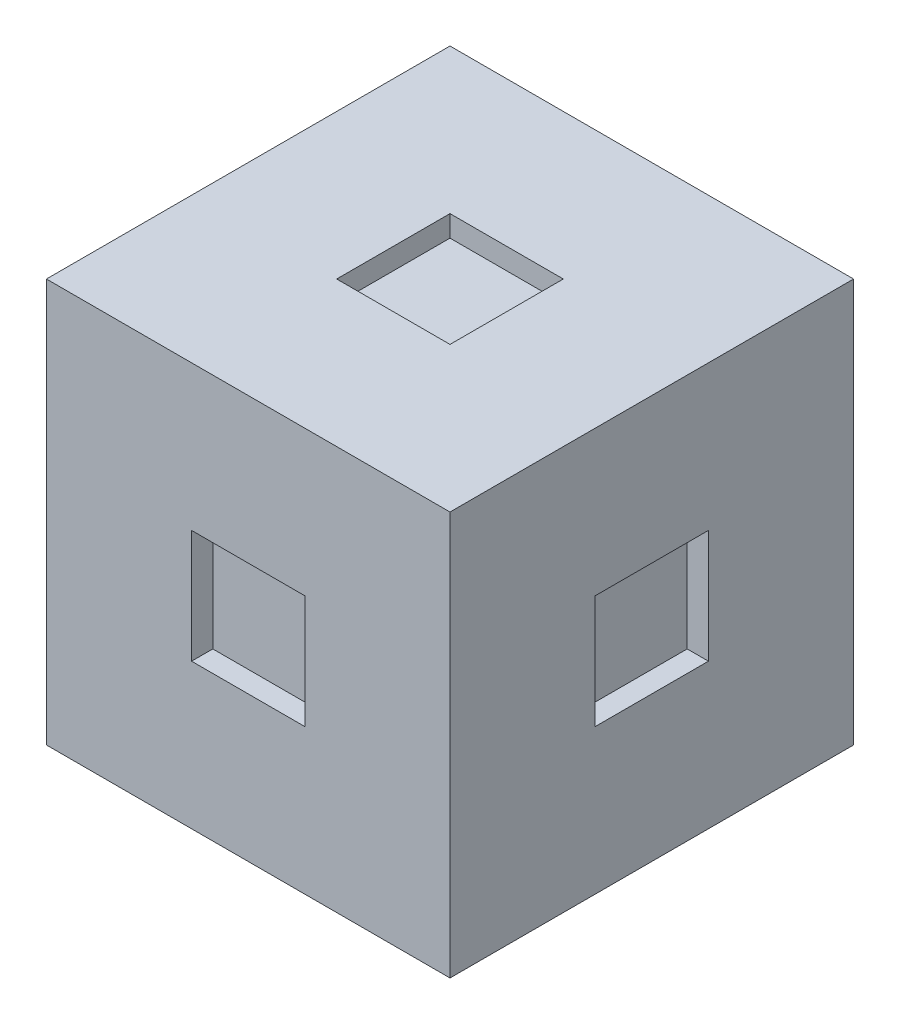
SolidWorks part; units mm, degrees
ref_plane "前视基准面" through (0, 0, 0) normal (0, 0, 1) x (1, 0, 0)
ref_plane "上视基准面" through (0, 0, 0) normal (0, 1, 0) x (1, 0, 0)
ref_plane "右视基准面" through (0, 0, 0) normal (1, 0, 0) x (0, 0, -1)
sketch "草图1" plane through (0, 0, 0) normal (0, 1, 0) x (1, 0, 0)
  line L1 (-28.5, 28.5) -> (28.5, 28.5)
  line L2 (-28.5, 28.5) -> (-28.5, -28.5)
  line L3 (-28.5, -28.5) -> (28.5, -28.5)
  line L4 (28.5, 28.5) -> (28.5, -28.5)
  line L5 (-28.5, 28.5) -> (28.5, -28.5) construction
  line L6 (-28.5, -28.5) -> (28.5, 28.5) construction
  point P0 (0, 0)
  dimension "D1" = 57
  dimension "D2" = 57
extrude "凸台-拉伸1" add sketch "草图1" along normal blind 57
sketch "草图2" plane through (0, 0, 28.5) normal (0, 0, 1) x (1, 0, 0)
  line L0 (-28.5, 57) -> (28.5, 0) construction
  line L1 (28.5, 57) -> (-28.5, 0) construction
  line L3 (-8, 36.5) -> (8, 36.5)
  line L4 (-8, 36.5) -> (-8, 20.5)
  line L5 (-8, 20.5) -> (8, 20.5)
  line L6 (8, 36.5) -> (8, 20.5)
  line L7 (-8, 36.5) -> (8, 20.5) construction
  line L8 (-8, 20.5) -> (8, 36.5) construction
  point P8 (0, 28.5)
  dimension "D1" = 16
extrude "切除-拉伸1" cut sketch "草图2" against normal blind 3
sketch "草图3" plane through (28.5, 0, 0) normal (1, 0, 0) x (0, 0, -1)
  line L0 (-28.5, 57) -> (28.5, 0) construction
  line L1 (28.5, 57) -> (-28.5, 0) construction
  line L3 (-8, 36.5) -> (8, 36.5)
  line L4 (-8, 36.5) -> (-8, 20.5)
  line L5 (-8, 20.5) -> (8, 20.5)
  line L6 (8, 36.5) -> (8, 20.5)
  line L7 (-8, 36.5) -> (8, 20.5) construction
  line L8 (-8, 20.5) -> (8, 36.5) construction
  point P8 (0, 28.5)
  dimension "D1" = 16
  dimension "D2" = 16
extrude "切除-拉伸2" cut sketch "草图3" against normal blind 3
sketch "草图4" plane through (0, 0, -28.5) normal (0, 0, -1) x (-1, 0, 0)
  line L0 (-28.5, 57) -> (28.5, 0) construction
  line L1 (28.5, 57) -> (-28.5, 0) construction
  line L3 (-8, 36.5) -> (8, 36.5)
  line L4 (-8, 36.5) -> (-8, 20.5)
  line L5 (-8, 20.5) -> (8, 20.5)
  line L6 (8, 36.5) -> (8, 20.5)
  line L7 (-8, 36.5) -> (8, 20.5) construction
  line L8 (-8, 20.5) -> (8, 36.5) construction
  point P8 (0, 28.5)
  dimension "D1" = 16
extrude "切除-拉伸3" cut sketch "草图4" against normal blind 3
sketch "草图5" plane through (-28.5, 0, 0) normal (-1, 0, 0) x (0, 0, 1)
  line L0 (-28.5, 57) -> (28.5, 0) construction
  line L1 (28.5, 57) -> (-28.5, 0) construction
  line L3 (-8, 36.5) -> (8, 36.5)
  line L4 (-8, 36.5) -> (-8, 20.5)
  line L5 (-8, 20.5) -> (8, 20.5)
  line L6 (8, 36.5) -> (8, 20.5)
  line L7 (-8, 36.5) -> (8, 20.5) construction
  line L8 (-8, 20.5) -> (8, 36.5) construction
  point P8 (0, 28.5)
  dimension "D1" = 16
  dimension "D2" = 16
extrude "切除-拉伸4" cut sketch "草图5" against normal blind 3
sketch "草图6" plane through (0, 57, 0) normal (0, 1, 0) x (1, 0, 0)
  line L0 (-28.5, 28.5) -> (28.5, -28.5) construction
  line L1 (28.5, 28.5) -> (-28.5, -28.5) construction
  line L3 (-8, 8) -> (8, 8)
  line L4 (-8, 8) -> (-8, -8)
  line L5 (-8, -8) -> (8, -8)
  line L6 (8, 8) -> (8, -8)
  line L7 (-8, 8) -> (8, -8) construction
  line L8 (-8, -8) -> (8, 8) construction
  point P8 (0, 0)
  dimension "D1" = 16
extrude "切除-拉伸5" cut sketch "草图6" against normal blind 3
sketch "草图7" plane through (0, 0, 0) normal (0, -1, 0) x (1, 0, 0)
  line L4 (-8, -8) -> (8, -8)
  line L5 (8, -8) -> (8, 8)
  line L6 (8, 8) -> (-8, 8)
  line L7 (-8, 8) -> (-8, -8)
  line L8 (-8, -8) -> (8, -8)
  line L9 (8, -8) -> (8, 8)
  line L10 (8, 8) -> (-8, 8)
  line L11 (-8, 8) -> (-8, -8)
  dimension "D1" = 0
extrude "切除-拉伸6" cut sketch "草图7" against normal blind 3
